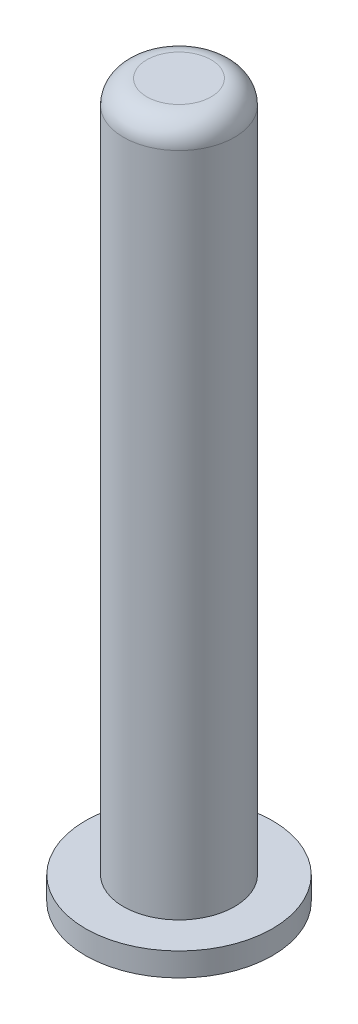
SolidWorks part; units mm, degrees
ref_plane "Front Plane" through (0, 0, 0) normal (0, 0, 1) x (1, 0, 0)
ref_plane "Top Plane" through (0, 0, 0) normal (0, 1, 0) x (1, 0, 0)
ref_plane "Right Plane" through (0, 0, 0) normal (1, 0, 0) x (0, 0, -1)
sketch "Sketch1" plane through (0, 0, 0) normal (0, 1, 0) x (1, 0, 0)
  circle A0 centre (0, 0) radius 4.75
extrude "Boss-Extrude1" add sketch "Sketch1" along normal blind 59
sketch "Sketch2" plane through (0, 0, 0) normal (0, -1, 0) x (-1, 0, 0)
  circle A0 centre (0, 0) radius 8
extrude "Boss-Extrude2" add sketch "Sketch2" along normal blind 2
fillet "Fillet1" radius 2 1 edges at (0, 59, 4.75)
